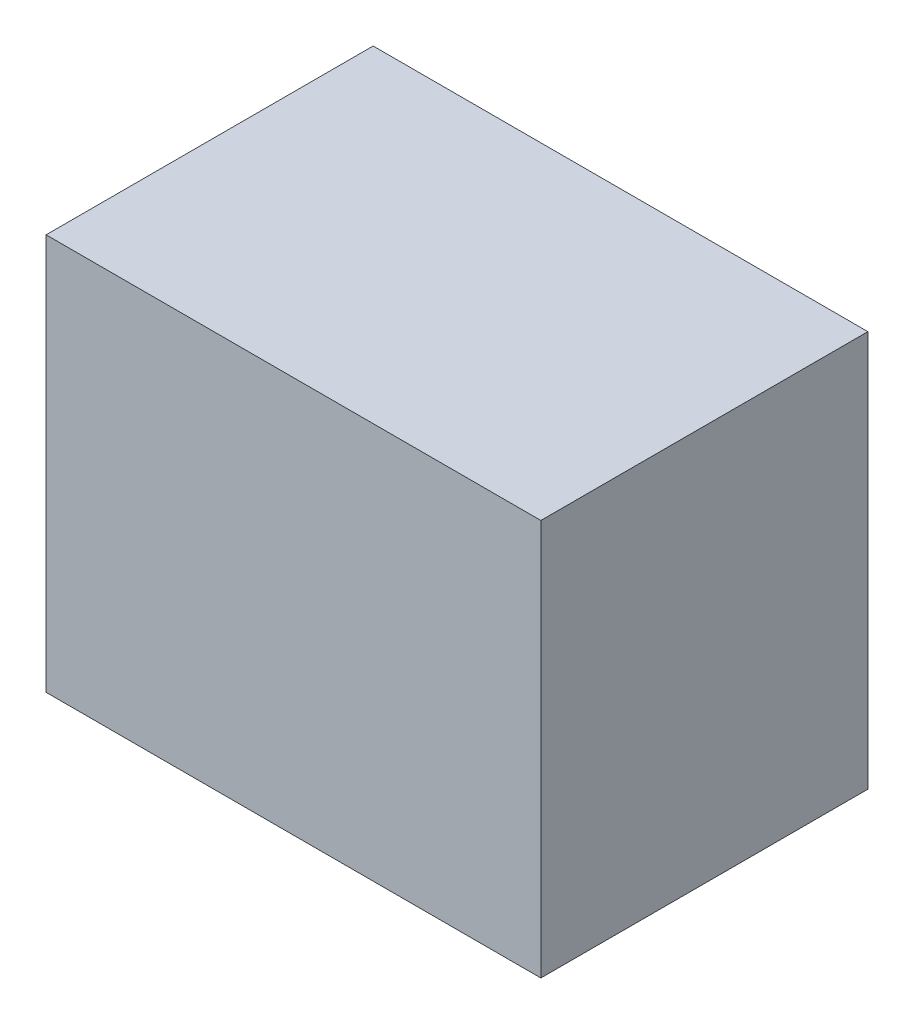
SolidWorks part; units mm, degrees
ref_plane "Front Plane" through (0, 0, 0) normal (0, 0, 1) x (1, 0, 0)
ref_plane "Top Plane" through (0, 0, 0) normal (0, 1, 0) x (1, 0, 0)
ref_plane "Right Plane" through (0, 0, 0) normal (1, 0, 0) x (0, 0, -1)
sketch "Sketch1" plane through (0, 0, 0) normal (0, 1, 0) x (1, 0, 0)
  line L1 (-250, -165.2542) -> (250, -165.2542)
  line L2 (-250, -165.2542) -> (-250, 165.2542)
  line L3 (-250, 165.2542) -> (250, 165.2542)
  line L4 (250, -165.2542) -> (250, 165.2542)
  line L5 (-250, -165.2542) -> (250, 165.2542) construction
  line L6 (-250, 165.2542) -> (250, -165.2542) construction
  point P0 (0, 0)
  dimension "D1" = 500
extrude "Boss-Extrude1" add sketch "Sketch1" along normal blind 400.456
